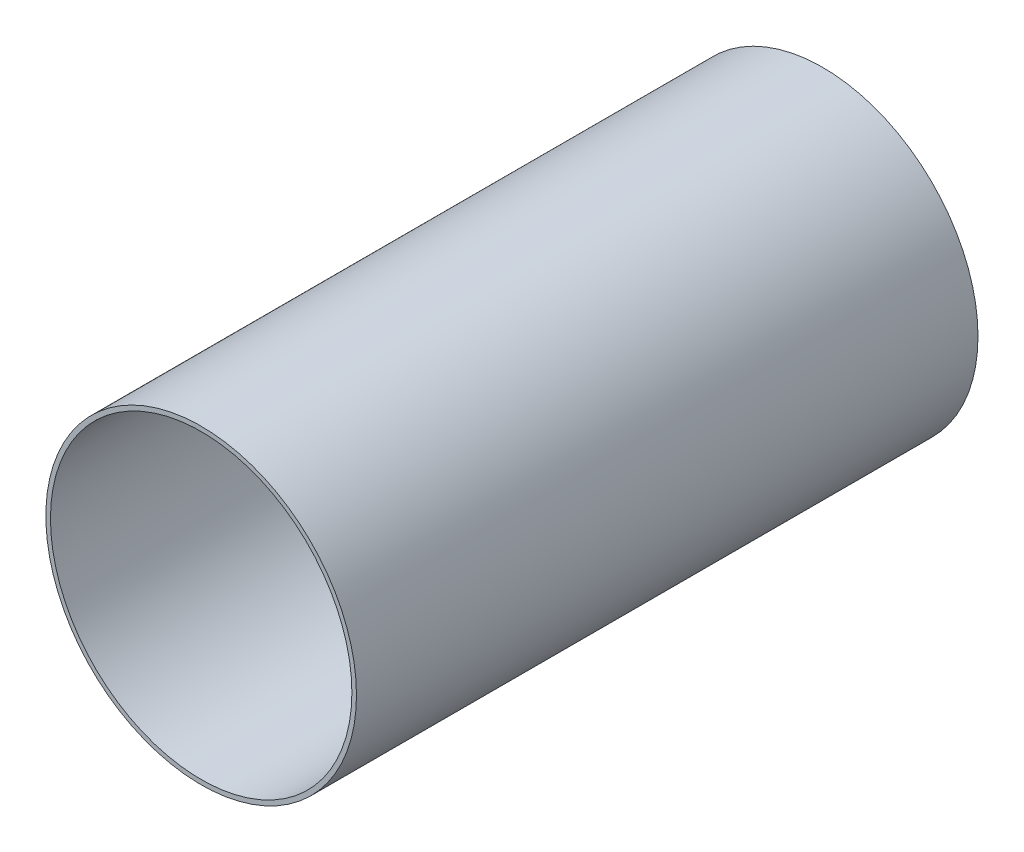
SolidWorks part; units mm, degrees
ref_plane "Front Plane" through (0, 0, 0) normal (0, 0, 1) x (1, 0, 0)
ref_plane "Top Plane" through (0, 0, 0) normal (0, 1, 0) x (1, 0, 0)
ref_plane "Right Plane" through (0, 0, 0) normal (1, 0, 0) x (0, 0, -1)
sketch "Sketch1" plane through (0, 0, 0) normal (0, 0, 1) x (1, 0, 0)
  circle A0 centre (0, 0) radius 63.4746
  circle A1 centre (0, 0) radius 61.595
  dimension "D1" = 123.19
  dimension "D2" = 126.9492
extrude "Boss-Extrude1" add sketch "Sketch1" along normal mid plane 254
equation "\"AIRFRAME_OD\"= 5.15in"
equation "\"AIRFRAME_ID\"= 4.99in"
equation "\"FLAT_T\"= 0.125in"
equation "\"NOSE_EXP_L\"= 27in"
equation "\"NOSE_SHOULDER_L\"= 5in"
equation "\"MAIN_L\"= 30in"
equation "\"RECO_COUP_L\"= 10in"
equation "\"RECO_SWITCH_L\"= 2in"
equation "\"DROGUE_L\"= 20in"
equation "\"ATS_FORE_COUP_L\"= 5.5in"
equation "\"ATS_AFT_COUP_L\"= 4.5in"
equation "\"LOWER_L\"= 30in"
equation "\"FIN_N\"= 4"
equation "\"CR_AFT_X\"= 0.5in"
equation "\"CR_FORE_X\"= 9.25in"
equation "\"D1@Sketch1\"=\"COUPLER_ID\""
equation "\"D2@Sketch1\"=\"COUPLER_OD\""
equation "\"D1@Boss-Extrude1\"=\"RECO_COUP_L\""
equation "\"FIN_ROOT\"= 8in"
equation "\"FIN_X\"= 0.75in"
equation "\"MOTOR_OD\"= 3.091in"
equation "\"MOTOR_ID\"= 3.00in"
equation "\"COUPLER_OD\"= 4.998in"
equation "\"COUPLER_ID\"= 4.85in"
equation "\"RECO_ROD_X\"= 3.5in"
equation "\"ATS_ROD_X\"= 3.75in"
equation "\"MOTOR_L\"= 14in"
equation "\"MOTOR_LOWER_X\"= 2in"
